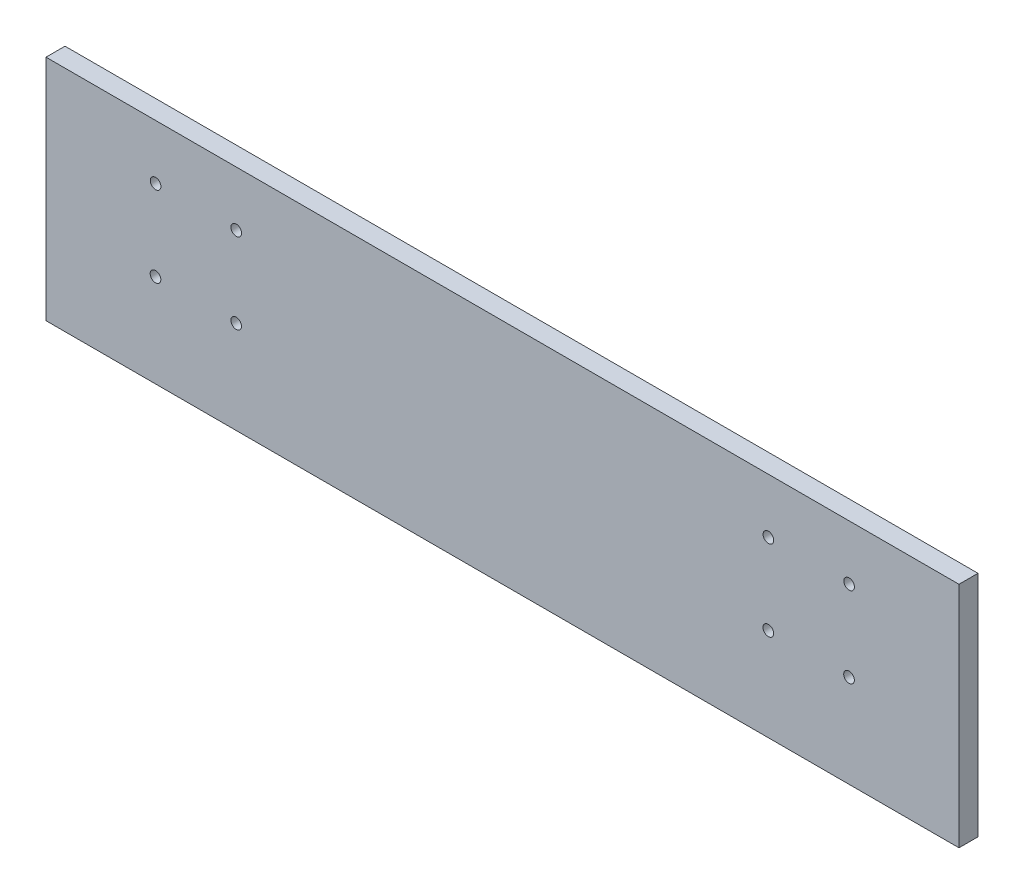
SolidWorks part; units mm, degrees
ref_plane "Front Plane" through (0, 0, 0) normal (0, 0, 1) x (1, 0, 0)
ref_plane "Top Plane" through (0, 0, 0) normal (0, 1, 0) x (1, 0, 0)
ref_plane "Right Plane" through (0, 0, 0) normal (1, 0, 0) x (0, 0, -1)
sketch "Sketch1" plane through (0, 0, 0) normal (0, 0, 1) x (1, 0, 0)
  line L1 (0, 0) -> (304.8, 0)
  line L2 (0, 0) -> (0, 76.2)
  line L3 (0, 76.2) -> (304.8, 76.2)
  line L4 (304.8, 0) -> (304.8, 76.2)
  dimension "D1" = 76.2
  dimension "D2" = 304.8
extrude "Boss-Extrude1" add sketch "Sketch1" along normal blind 6.35
sketch "Sketch2" plane through (0, 0, 0) normal (0, 0, -1) x (-1, 0, 0)
  circle A0 centre (-268.1166, 57.9371) radius 1.778
  circle A1 centre (-241.1759, 57.9596) radius 1.778
  circle A2 centre (-241.1534, 31.0188) radius 1.778
  circle A3 centre (-268.0941, 30.9963) radius 1.778
  circle A4 centre (-36.5789, 57.9596) radius 1.778
  circle A5 centre (-63.5196, 57.9371) radius 1.778
  circle A6 centre (-63.4971, 30.9963) radius 1.778
  circle A7 centre (-36.5564, 31.0188) radius 1.778
extrude "Cut-Extrude1" cut sketch "Sketch2" against normal blind 10.16
